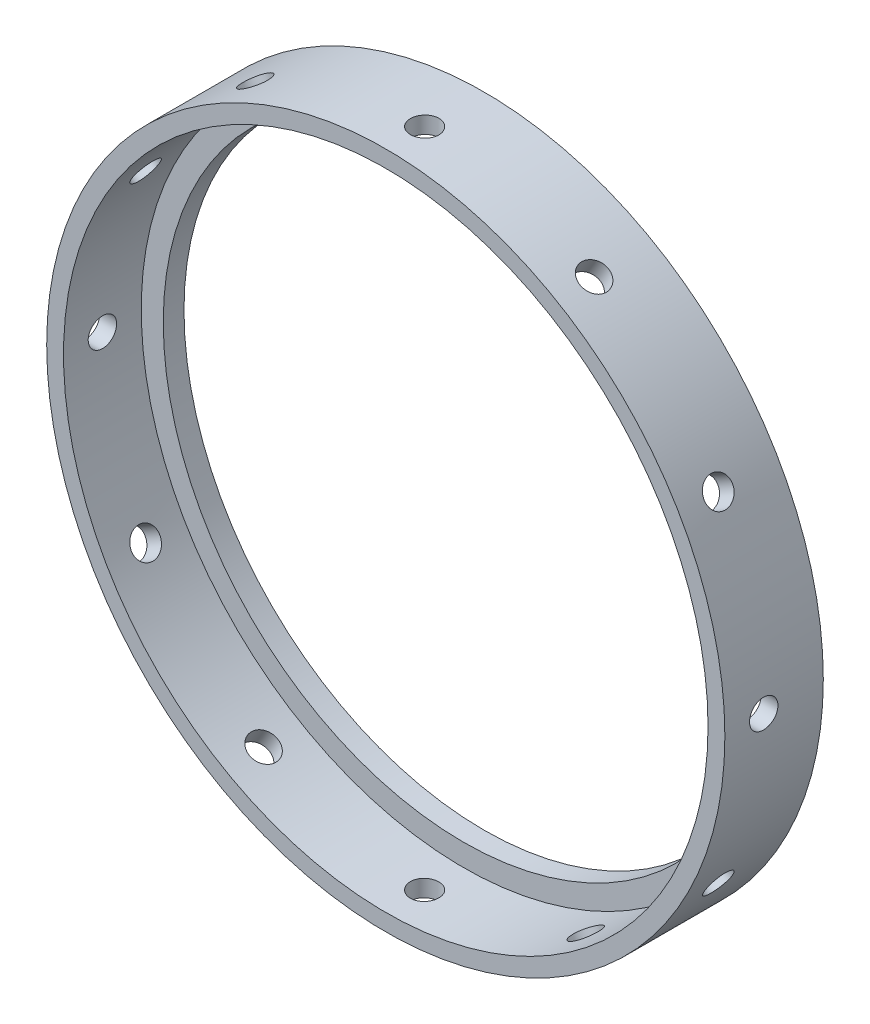
SolidWorks part; units mm, degrees
ref_plane "Front Plane" through (0, 0, 0) normal (0, 0, 1) x (1, 0, 0)
ref_plane "Top Plane" through (0, 0, 0) normal (0, 1, 0) x (1, 0, 0)
ref_plane "Right Plane" through (0, 0, 0) normal (1, 0, 0) x (0, 0, -1)
sketch "Sketch1" plane through (0, 0, 0) normal (0, 0, 1) x (1, 0, 0)
  circle A0 centre (0, 0) radius 78.994
  circle A1 centre (0, 0) radius 83.1215
  dimension "D1" = 157.988
  dimension "D2" = 166.243
extrude "Boss-Extrude1" add sketch "Sketch1" along normal blind 19.05
sketch "Sketch2" plane through (0, 0, 0) normal (0, 1, 0) x (1, 0, 0)
  line L0 (78.994, 0) -> (-78.994, 0) construction
  line L1 (0, -2.0807) -> (0, -15.8358) construction
  circle A0 centre (0, -9.525) radius 3.4782
  dimension "D1" = 9.525
extrude "Cut-Extrude1" cut sketch "Sketch2" against normal through all
ref_axis "Axis1" through (0, 0, 2.0807) along (0, 0, 1)
pattern_circular "CirPattern1" count 12 over 360 about axis through (0, 0, 2.0807) along (0, 0, 1) of "Cut-Extrude1"
sketch "Sketch3" plane through (0, 0, 0) normal (0, 0, -1) x (-1, 0, 0)
  circle A0 centre (0, 0) radius 83.1215
  circle A1 centre (0, 0) radius 73.5965
  dimension "D1" = 166.243
  dimension "D2" = 147.193
extrude "Boss-Extrude2" add sketch "Sketch3" along normal blind 5.08
